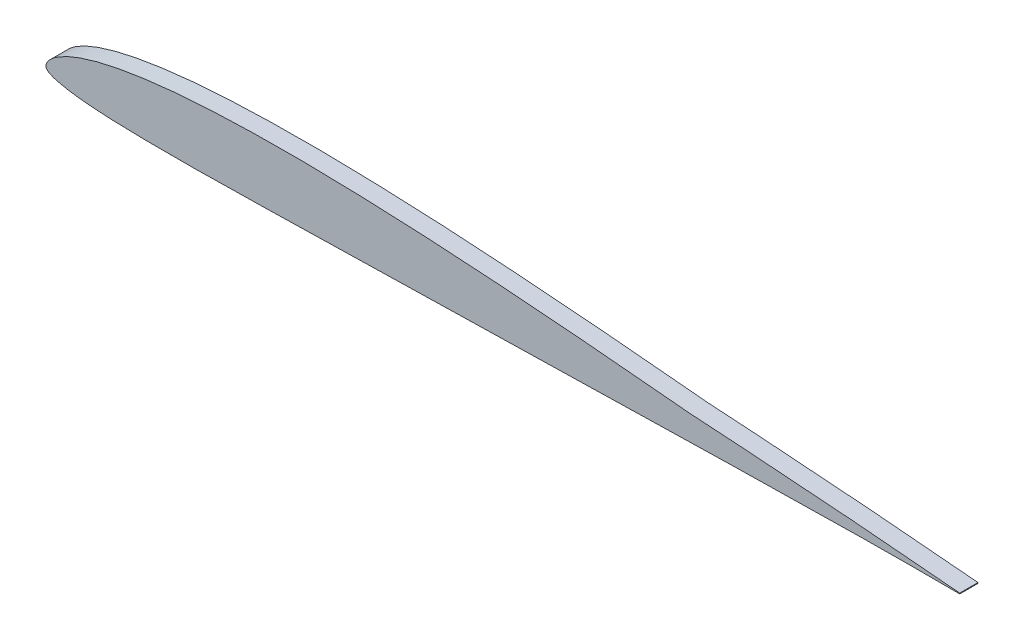
SolidWorks part; units mm, degrees
ref_plane "Front Plane" through (0, 0, 0) normal (0, 0, 1) x (1, 0, 0)
ref_plane "Top Plane" through (0, 0, 0) normal (0, 1, 0) x (1, 0, 0)
ref_plane "Right Plane" through (0, 0, 0) normal (1, 0, 0) x (0, 0, -1)
curve "Curve1"
  spline degree 3 poles (25.4, 0.0107, 0) (25.3506, 0.0152, 0) (25.2009, 0.0289, 0) (24.9376, 0.0531, 0) (24.6076, 0.082, 0) (24.2616, 0.1124, 0) (23.9125, 0.1431, 0) (23.5625, 0.1725, 0) (23.212, 0.2019, 0) (22.8613, 0.2307, 0) (22.5105, 0.2591, 0) (22.1596, 0.2869, 0) (21.8089, 0.314, 0) (21.4582, 0.3409, 0) (21.1077, 0.367, 0) (20.7573, 0.3928, 0) (20.407, 0.4182, 0) (20.0568, 0.4428, 0) (19.7068, 0.4673, 0) (19.3568, 0.4911, 0) (19.0069, 0.5145, 0) (18.6571, 0.5374, 0) (18.3335, 0.5583, 0) (18.0818, 0.5739, 0) (17.9246, 0.5843, 0) (17.8356, 0.5888, 0) (17.7472, 0.5983, 0) (17.5613, 0.6156, 0) (17.278, 0.6431, 0) (16.98, 0.6709, 0) (16.7137, 0.6956, 0) (16.4751, 0.7176, 0) (16.176, 0.7447, 0) (15.8267, 0.776, 0) (15.4701, 0.8073, 0) (15.1145, 0.838, 0) (14.7793, 0.8663, 0) (14.4495, 0.8936, 0) (14.1621, 0.9169, 0) (13.925, 0.9358, 0) (13.6642, 0.9563, 0) (13.3619, 0.9794, 0) (13.0103, 1.0056, 0) (12.659, 1.031, 0) (12.3077, 1.0554, 0) (11.9565, 1.0789, 0) (11.6054, 1.1014, 0) (11.2544, 1.1228, 0) (10.9034, 1.1432, 0) (10.5525, 1.1624, 0) (10.2016, 1.1803, 0) (9.8507, 1.197, 0) (9.5, 1.2123, 0) (9.1492, 1.2263, 0) (8.7986, 1.2386, 0) (8.448, 1.2494, 0) (8.0977, 1.2585, 0) (7.7474, 1.2658, 0) (7.3974, 1.2711, 0) (7.0475, 1.2745, 0) (6.6979, 1.2756, 0) (6.3485, 1.2744, 0) (5.9995, 1.2706, 0) (5.6509, 1.2642, 0) (5.3028, 1.2548, 0) (4.9554, 1.2422, 0) (4.6087, 1.2261, 0) (4.2629, 1.2062, 0) (3.9183, 1.1823, 0) (3.5751, 1.1536, 0) (3.2336, 1.12, 0) (2.8944, 1.0807, 0) (2.5581, 1.0351, 0) (2.2254, 0.9824, 0) (1.8975, 0.9214, 0) (1.5762, 0.8511, 0) (1.2643, 0.7698, 0) (0.9677, 0.6771, 0) (0.6972, 0.5737, 0) (0.4689, 0.4653, 0) (0.2948, 0.361, 0) (0.1747, 0.2696, 0) (0.0967, 0.1939, 0) (0.0471, 0.1311, 0) (0.0171, 0.0777, 0) (0.0019, 0.0319, 0) (-0.0016, -0.0085, 0) (0.0071, -0.0466, 0) (0.0322, -0.0832, 0) (0.0764, -0.1158, 0) (0.1405, -0.1489, 0) (0.2348, -0.1846, 0) (0.3747, -0.2244, 0) (0.5727, -0.265, 0) (0.8268, -0.3029, 0) (1.1218, -0.3343, 0) (1.4394, -0.3584, 0) (1.7684, -0.3763, 0) (2.1036, -0.389, 0) (2.4428, -0.3976, 0) (2.7846, -0.4031, 0) (3.1285, -0.4061, 0) (3.4739, -0.407, 0) (3.8205, -0.4061, 0) (4.168, -0.4035, 0) (4.5164, -0.3997, 0) (4.8654, -0.3948, 0) (5.2151, -0.389, 0) (5.5654, -0.3825, 0) (5.9165, -0.3755, 0) (6.2684, -0.368, 0) (6.621, -0.3604, 0) (6.9745, -0.3524, 0) (7.3287, -0.3442, 0) (7.6835, -0.336, 0) (8.039, -0.3276, 0) (8.3948, -0.3192, 0) (8.7511, -0.3108, 0) (9.1077, -0.3024, 0) (9.4646, -0.2939, 0) (9.8219, -0.2855, 0) (10.1795, -0.2771, 0) (10.5373, -0.2687, 0) (10.8952, -0.2603, 0) (11.2527, -0.252, 0) (11.6101, -0.2438, 0) (11.9672, -0.2355, 0) (12.3241, -0.2274, 0) (12.6807, -0.2193, 0) (13.0371, -0.2114, 0) (13.3934, -0.2033, 0) (13.6949, -0.1966, 0) (13.9592, -0.1908, 0) (14.1921, -0.1856, 0) (14.4749, -0.1792, 0) (14.7878, -0.1723, 0) (15.131, -0.1647, 0) (15.4754, -0.1569, 0) (15.8234, -0.1492, 0) (16.1349, -0.1423, 0) (16.4075, -0.1363, 0) (16.6379, -0.1313, 0) (16.9029, -0.1255, 0) (17.2072, -0.1189, 0) (17.4885, -0.1128, 0) (17.6791, -0.1088, 0) (17.7715, -0.1068, 0) (17.8501, -0.1053, 0) (18.0096, -0.1018, 0) (18.269, -0.0964, 0) (18.61, -0.0893, 0) (18.9621, -0.082, 0) (19.3141, -0.0749, 0) (19.666, -0.0678, 0) (20.0179, -0.0609, 0) (20.3698, -0.054, 0) (20.7219, -0.0473, 0) (21.074, -0.0408, 0) (21.4262, -0.0348, 0) (21.7784, -0.0292, 0) (22.1308, -0.0242, 0) (22.4832, -0.0197, 0) (22.8357, -0.0157, 0) (23.1883, -0.0125, 0) (23.5408, -0.0098, 0) (23.8935, -0.008, 0) (24.246, -0.0071, 0) (24.5963, -0.007, 0) (24.9308, -0.0084, 0) (25.198, -0.0096, 0) (25.3499, -0.0104, 0) (25.4, -0.0107, 0) knots 0 0 0 0 0.002901 0.008799 0.015478 0.022288 0.029131 0.035985 0.042847 0.049714 0.056581 0.063448 0.070313 0.077171 0.084031 0.090885 0.097737 0.104584 0.111432 0.118275 0.125116 0.131954 0.138793 0.144098 0.146709 0.148014 0.149313 0.151911 0.158945 0.165974 0.169425 0.174599 0.18 0.186998 0.195126 0.200949 0.20789 0.214818 0.220317 0.224762 0.228741 0.235631 0.242503 0.249376 0.256249 0.263115 0.269975 0.276837 0.283698 0.290553 0.297409 0.304262 0.311112 0.317958 0.324805 0.331647 0.338484 0.345319 0.352149 0.358974 0.365797 0.372613 0.37942 0.386225 0.393018 0.399801 0.406576 0.413331 0.420073 0.426793 0.433487 0.440154 0.446776 0.453353 0.459862 0.466294 0.472602 0.478718 0.484477 0.489534 0.493496 0.496331 0.498346 0.499841 0.500999 0.501915 0.502649 0.503345 0.504158 0.505185 0.506526 0.508376 0.511074 0.515031 0.520197 0.526109 0.532386 0.538838 0.545393 0.552019 0.558693 0.565404 0.572145 0.578909 0.585689 0.592488 0.599298 0.60612 0.612956 0.619809 0.626673 0.633554 0.640451 0.647364 0.654291 0.661227 0.668172 0.675126 0.682086 0.689049 0.69602 0.703 0.709987 0.71697 0.723948 0.73092 0.73789 0.744856 0.751814 0.758769 0.765721 0.77267 0.776424 0.78119 0.786305 0.792978 0.79951 0.806399 0.81314 0.819881 0.824633 0.829103 0.833367 0.840145 0.84692 0.849831 0.851305 0.852333 0.85443 0.860642 0.867519 0.87439 0.881257 0.888123 0.894989 0.901857 0.908727 0.915597 0.922469 0.929344 0.936217 0.943092 0.949972 0.956848 0.963729 0.970609 0.97749 0.984361 0.991109 0.997067 1 1 1 1
sketch "Sketch2" plane through (0, 0, 0) normal (0, 0, 1) x (1, 0, 0)
  line L0 (64.7182, -2.4991) -> (64.7182, -2.5635)
  line L1 (127, 0.0536) -> (127, -0.0536)
  spline S0 degree 3 poles (-80.1469, -1996.7005) (74.4105, -0.3887) (49.5476, -2.2151) (24.9376, 0.0531) (24.6076, 0.082) (24.2616, 0.1124) (23.9125, 0.1431) (23.5625, 0.1725) (23.212, 0.2019) (22.8613, 0.2307) (22.5105, 0.2591) (22.1596, 0.2869) (21.8089, 0.314) (21.4582, 0.3409) (21.1077, 0.367) (20.7573, 0.3928) (20.407, 0.4182) (20.0568, 0.4428) (19.7068, 0.4673) (19.3568, 0.4911) (19.0069, 0.5145) (18.6571, 0.5374) (18.3335, 0.5583) (18.0818, 0.5739) (17.9246, 0.5843) (17.8356, 0.5888) (17.7472, 0.5983) (17.5613, 0.6156) (17.278, 0.6431) (16.98, 0.6709) (16.7137, 0.6956) (16.4751, 0.7176) (16.176, 0.7447) (15.8267, 0.776) (15.4701, 0.8073) (15.1145, 0.838) (14.7793, 0.8663) (14.4495, 0.8936) (14.1621, 0.9169) (13.925, 0.9358) (13.6642, 0.9563) (13.3619, 0.9794) (13.0103, 1.0056) (12.659, 1.031) (12.1907, 1.0635) (11.7225, 1.0942) (11.2544, 1.1228) (10.9034, 1.1432) (10.4356, 1.1688) (9.9677, 1.1919) (9.5, 1.2123) (9.1492, 1.2263) (8.7986, 1.2386) (8.448, 1.2494) (8.0977, 1.2585) (7.7474, 1.2658) (7.3974, 1.2711) (7.0475, 1.2745) (6.6979, 1.2756) (6.3485, 1.2744) (5.9995, 1.2706) (5.6509, 1.2642) (5.3028, 1.2548) (4.9554, 1.2422) (4.6087, 1.2261) (4.2629, 1.2062) (3.9183, 1.1823) (3.5751, 1.1536) (3.2336, 1.12) (2.8944, 1.0807) (2.5581, 1.0351) (2.2254, 0.9824) (1.8975, 0.9214) (1.5762, 0.8511) (1.2643, 0.7698) (0.9677, 0.6771) (0.6972, 0.5737) (0.4689, 0.4653) (0.2948, 0.361) (0.1747, 0.2696) (0.0967, 0.1939) (0.0471, 0.1311) (0.0171, 0.0777) (0.0019, 0.0319) (-0.0016, -0.0085) (0.0071, -0.0466) (0.0322, -0.0832) (0.0764, -0.1158) (0.1405, -0.1489) (0.2348, -0.1846) (0.3747, -0.2244) (0.5727, -0.265) (0.8268, -0.3029) (1.1218, -0.3343) (1.4394, -0.3584) (1.7684, -0.3763) (2.1036, -0.389) (2.4428, -0.3976) (2.7846, -0.4031) (3.1285, -0.4061) (3.4739, -0.407) (3.8205, -0.4061) (4.168, -0.4035) (4.5164, -0.3997) (4.8654, -0.3948) (5.2151, -0.389) (5.5654, -0.3825) (5.9165, -0.3755) (6.2684, -0.368) (6.621, -0.3604) (6.9745, -0.3524) (7.3287, -0.3442) (7.8022, -0.3332) (8.2764, -0.322) (8.7511, -0.3108) (9.1077, -0.3024) (9.4646, -0.2939) (9.8219, -0.2855) (10.1795, -0.2771) (10.5373, -0.2687) (10.8952, -0.2603) (11.2527, -0.252) (11.6101, -0.2438) (11.9672, -0.2355) (12.3241, -0.2274) (12.6807, -0.2193) (13.0371, -0.2114) (13.3934, -0.2033) (13.6949, -0.1966) (14.0466, -0.1889) (14.3934, -0.181) (14.7878, -0.1723) (15.131, -0.1647) (15.4754, -0.1569) (15.8234, -0.1492) (16.1349, -0.1423) (16.4075, -0.1363) (16.6379, -0.1313) (16.9029, -0.1255) (17.2072, -0.1189) (17.4885, -0.1128) (17.6791, -0.1088) (17.7715, -0.1068) (17.8501, -0.1053) (18.0096, -0.1018) (18.269, -0.0964) (18.61, -0.0893) (18.9621, -0.082) (19.3141, -0.0749) (19.666, -0.0678) (20.0179, -0.0609) (20.3698, -0.054) (20.7219, -0.0473) (21.074, -0.0408) (21.4262, -0.0348) (21.8959, -0.0274) (22.3658, -0.021) (22.8357, -0.0157) (23.1883, -0.0125) (23.5408, -0.0098) (23.8935, -0.008) (24.246, -0.0071) (24.5963, -0.007) (24.9308, -0.0084) (48.8353, -0.1171) (72.6037, -4.5166) (105.9787, 1997.8631) knots -1.431006 -1.431006 -1.431006 -1.431006 0.002901 0.008799 0.015478 0.022288 0.029131 0.035985 0.042847 0.049714 0.056581 0.063448 0.070313 0.077171 0.084031 0.090885 0.097737 0.104584 0.111432 0.118275 0.125116 0.131954 0.138793 0.144098 0.146709 0.148014 0.149313 0.151911 0.158945 0.165974 0.169425 0.174599 0.18 0.186998 0.195126 0.200949 0.20789 0.214818 0.220317 0.224762 0.228741 0.235631 0.242503 0.249376 0.256249 0.269975 0.276837 0.283698 0.290553 0.304262 0.311112 0.317958 0.324805 0.331647 0.338484 0.345319 0.352149 0.358974 0.365797 0.372613 0.37942 0.386225 0.393018 0.399801 0.406576 0.413331 0.420073 0.426793 0.433487 0.440154 0.446776 0.453353 0.459862 0.466294 0.472602 0.478718 0.484477 0.489534 0.493496 0.496331 0.498346 0.499841 0.500999 0.501915 0.502649 0.503345 0.504158 0.505185 0.506526 0.508376 0.511074 0.515031 0.520197 0.526109 0.532386 0.538838 0.545393 0.552019 0.558693 0.565404 0.572145 0.578909 0.585689 0.592488 0.599298 0.60612 0.612956 0.619809 0.626673 0.633554 0.640451 0.647364 0.654291 0.668172 0.675126 0.682086 0.689049 0.69602 0.703 0.709987 0.71697 0.723948 0.73092 0.73789 0.744856 0.751814 0.758769 0.765721 0.77267 0.776424 0.786305 0.792978 0.79951 0.806399 0.81314 0.819881 0.824633 0.829103 0.833367 0.840145 0.84692 0.849831 0.851305 0.852333 0.85443 0.860642 0.867519 0.87439 0.881257 0.888123 0.894989 0.901857 0.908727 0.915597 0.922469 0.929344 0.943092 0.949972 0.956848 0.963729 0.970609 0.97749 0.984361 0.991109 0.997067 2.383465 2.383465 2.383465 2.383465 only from (25.4, 0.0107) to (25.4, -0.0107) construction
  spline S1 degree 3 poles (25.4, 0.0107) (25.3506, 0.0152) (25.2009, 0.0289) (24.9376, 0.0531) (24.6076, 0.082) (24.2616, 0.1124) (23.9125, 0.1431) (23.5625, 0.1725) (23.212, 0.2019) (22.8613, 0.2307) (22.5105, 0.2591) (22.1596, 0.2869) (21.8089, 0.314) (21.4582, 0.3409) (21.1077, 0.367) (20.7573, 0.3928) (20.407, 0.4182) (20.0568, 0.4428) (19.7068, 0.4673) (19.3568, 0.4911) (19.0069, 0.5145) (18.6571, 0.5374) (18.3335, 0.5583) (18.0818, 0.5739) (17.9246, 0.5843) (17.8356, 0.5888) (17.7472, 0.5983) (17.5613, 0.6156) (17.278, 0.6431) (16.98, 0.6709) (16.7137, 0.6956) (16.4751, 0.7176) (16.176, 0.7447) (15.8267, 0.776) (15.4701, 0.8073) (15.1145, 0.838) (14.7793, 0.8663) (14.4495, 0.8936) (14.1621, 0.9169) (13.925, 0.9358) (13.6642, 0.9563) (13.3619, 0.9794) (13.0103, 1.0056) (12.659, 1.031) (12.1907, 1.0635) (11.7225, 1.0942) (11.2544, 1.1228) (10.9034, 1.1432) (10.4356, 1.1688) (9.9677, 1.1919) (9.5, 1.2123) (9.1492, 1.2263) (8.7986, 1.2386) (8.448, 1.2494) (8.0977, 1.2585) (7.7474, 1.2658) (7.3974, 1.2711) (7.0475, 1.2745) (6.6979, 1.2756) (6.3485, 1.2744) (5.9995, 1.2706) (5.6509, 1.2642) (5.3028, 1.2548) (4.9554, 1.2422) (4.6087, 1.2261) (4.2629, 1.2062) (3.9183, 1.1823) (3.5751, 1.1536) (3.2336, 1.12) (2.8944, 1.0807) (2.5581, 1.0351) (2.2254, 0.9824) (1.8975, 0.9214) (1.5762, 0.8511) (1.2643, 0.7698) (0.9677, 0.6771) (0.6972, 0.5737) (0.4689, 0.4653) (0.2948, 0.361) (0.1747, 0.2696) (0.0967, 0.1939) (0.0471, 0.1311) (0.0171, 0.0777) (0.0019, 0.0319) (-0.0016, -0.0085) (0.0071, -0.0466) (0.0322, -0.0832) (0.0764, -0.1158) (0.1405, -0.1489) (0.2348, -0.1846) (0.3747, -0.2244) (0.5727, -0.265) (0.8268, -0.3029) (1.1218, -0.3343) (1.4394, -0.3584) (1.7684, -0.3763) (2.1036, -0.389) (2.4428, -0.3976) (2.7846, -0.4031) (3.1285, -0.4061) (3.4739, -0.407) (3.8205, -0.4061) (4.168, -0.4035) (4.5164, -0.3997) (4.8654, -0.3948) (5.2151, -0.389) (5.5654, -0.3825) (5.9165, -0.3755) (6.2684, -0.368) (6.621, -0.3604) (6.9745, -0.3524) (7.3287, -0.3442) (7.8022, -0.3332) (8.2764, -0.322) (8.7511, -0.3108) (9.1077, -0.3024) (9.4646, -0.2939) (9.8219, -0.2855) (10.1795, -0.2771) (10.5373, -0.2687) (10.8952, -0.2603) (11.2527, -0.252) (11.6101, -0.2438) (11.9672, -0.2355) (12.3241, -0.2274) (12.6807, -0.2193) (13.0371, -0.2114) (13.3934, -0.2033) (13.6949, -0.1966) (14.0466, -0.1889) (14.3934, -0.181) (14.7878, -0.1723) (15.131, -0.1647) (15.4754, -0.1569) (15.8234, -0.1492) (16.1349, -0.1423) (16.4075, -0.1363) (16.6379, -0.1313) (16.9029, -0.1255) (17.2072, -0.1189) (17.4885, -0.1128) (17.6791, -0.1088) (17.7715, -0.1068) (17.8501, -0.1053) (18.0096, -0.1018) (18.269, -0.0964) (18.61, -0.0893) (18.9621, -0.082) (19.3141, -0.0749) (19.666, -0.0678) (20.0179, -0.0609) (20.3698, -0.054) (20.7219, -0.0473) (21.074, -0.0408) (21.4262, -0.0348) (21.8959, -0.0274) (22.3658, -0.021) (22.8357, -0.0157) (23.1883, -0.0125) (23.5408, -0.0098) (23.8935, -0.008) (24.246, -0.0071) (24.5963, -0.007) (24.9308, -0.0084) (25.198, -0.0096) (25.3499, -0.0104) (25.4, -0.0107) knots 0 0 0 0 0.002901 0.008799 0.015478 0.022288 0.029131 0.035985 0.042847 0.049714 0.056581 0.063448 0.070313 0.077171 0.084031 0.090885 0.097737 0.104584 0.111432 0.118275 0.125116 0.131954 0.138793 0.144098 0.146709 0.148014 0.149313 0.151911 0.158945 0.165974 0.169425 0.174599 0.18 0.186998 0.195126 0.200949 0.20789 0.214818 0.220317 0.224762 0.228741 0.235631 0.242503 0.249376 0.256249 0.269975 0.276837 0.283698 0.290553 0.304262 0.311112 0.317958 0.324805 0.331647 0.338484 0.345319 0.352149 0.358974 0.365797 0.372613 0.37942 0.386225 0.393018 0.399801 0.406576 0.413331 0.420073 0.426793 0.433487 0.440154 0.446776 0.453353 0.459862 0.466294 0.472602 0.478718 0.484477 0.489534 0.493496 0.496331 0.498346 0.499841 0.500999 0.501915 0.502649 0.503345 0.504158 0.505185 0.506526 0.508376 0.511074 0.515031 0.520197 0.526109 0.532386 0.538838 0.545393 0.552019 0.558693 0.565404 0.572145 0.578909 0.585689 0.592488 0.599298 0.60612 0.612956 0.619809 0.626673 0.633554 0.640451 0.647364 0.654291 0.668172 0.675126 0.682086 0.689049 0.69602 0.703 0.709987 0.71697 0.723948 0.73092 0.73789 0.744856 0.751814 0.758769 0.765721 0.77267 0.776424 0.786305 0.792978 0.79951 0.806399 0.81314 0.819881 0.824633 0.829103 0.833367 0.840145 0.84692 0.849831 0.851305 0.852333 0.85443 0.860642 0.867519 0.87439 0.881257 0.888123 0.894989 0.901857 0.908727 0.915597 0.922469 0.929344 0.943092 0.949972 0.956848 0.963729 0.970609 0.97749 0.984361 0.991109 0.997067 1 1 1 1
  spline S2 degree 3 poles (127, 0.0536) (126.7532, 0.0761) (126.0046, 0.1443) (124.6879, 0.2657) (123.038, 0.4099) (121.3078, 0.5622) (119.5626, 0.7154) (117.8125, 0.8626) (116.0602, 1.0096) (114.3066, 1.1533) (112.5524, 1.2954) (110.7981, 1.4344) (109.0444, 1.5698) (107.2911, 1.7045) (105.5386, 1.8351) (103.7864, 1.9642) (102.0351, 2.0908) (100.2841, 2.214) (98.5339, 2.3364) (96.7839, 2.4555) (95.0347, 2.5723) (93.2856, 2.6871) (91.6673, 2.7916) (90.4092, 2.8696) (89.6232, 2.9215) (89.1782, 2.9441) (88.7362, 2.9915) (87.8065, 3.0778) (86.3898, 3.2155) (84.9001, 3.3545) (83.5684, 3.478) (82.3753, 3.5879) (80.8802, 3.7236) (79.1336, 3.8802) (77.3507, 4.0366) (75.5725, 4.1898) (73.8963, 4.3315) (72.2474, 4.4682) (70.8107, 4.5845) (69.625, 4.6789) (68.3208, 4.7815) (66.8096, 4.8971) (65.0517, 5.0279) (63.2949, 5.1548) (60.9536, 5.3176) (58.6126, 5.471) (56.2721, 5.6142) (54.5172, 5.7159) (52.1778, 5.8439) (49.8387, 5.9596) (47.4998, 6.0617) (45.7461, 6.1315) (43.9929, 6.1932) (42.2402, 6.247) (40.4883, 6.2924) (38.7372, 6.3291) (36.987, 6.3557) (35.2377, 6.3726) (33.4894, 6.3781) (31.7426, 6.3719) (29.9976, 6.3531) (28.2547, 6.321) (26.5142, 6.274) (24.7768, 6.2109) (23.0433, 6.1307) (21.3143, 6.0312) (19.5913, 5.9114) (17.8753, 5.7682) (16.1681, 5.6002) (14.4722, 5.4034) (12.7903, 5.1755) (11.1272, 4.9119) (9.4877, 4.6072) (7.881, 4.2554) (6.3217, 3.8492) (4.8384, 3.3854) (3.4862, 2.8684) (2.3443, 2.3263) (1.4738, 1.805) (0.8733, 1.3482) (0.4835, 0.9696) (0.2355, 0.6556) (0.0854, 0.3886) (0.0093, 0.1593) (-0.0082, -0.0427) (0.0354, -0.2332) (0.1608, -0.4161) (0.3818, -0.5789) (0.7024, -0.7445) (1.1738, -0.9231) (1.8733, -1.1219) (2.8634, -1.3251) (4.1342, -1.5144) (5.6088, -1.6713) (7.1969, -1.7921) (8.842, -1.8815) (10.5181, -1.945) (12.2138, -1.9881) (13.9231, -2.0156) (15.6423, -2.0306) (17.3693, -2.0352) (19.1023, -2.0304) (20.8402, -2.0177) (22.5819, -1.9987) (24.3271, -1.9739) (26.0754, -1.9449) (27.8272, -1.9125) (29.5827, -1.8776) (31.342, -1.84) (33.1051, -1.8019) (34.8723, -1.7618) (36.6433, -1.721) (39.0109, -1.666) (41.3818, -1.6098) (43.7556, -1.5538) (45.5386, -1.5118) (47.323, -1.4696) (49.1093, -1.4276) (50.8974, -1.3853) (52.6867, -1.3435) (54.4758, -1.3017) (56.2636, -1.2601) (58.0503, -1.2192) (59.836, -1.1776) (61.6205, -1.1372) (63.4036, -1.0967) (65.1856, -1.0568) (66.9668, -1.0167) (68.4747, -0.9832) (70.2328, -0.9443) (71.9672, -0.9051) (73.939, -0.8615) (75.6551, -0.8234) (77.3771, -0.7847) (79.117, -0.7461) (80.6743, -0.7116) (82.0377, -0.6816) (83.1895, -0.6565) (84.5144, -0.6274) (86.0361, -0.5947) (87.4423, -0.5642) (88.3955, -0.5441) (88.8577, -0.534) (89.2506, -0.5265) (90.048, -0.509) (91.3451, -0.4819) (93.0499, -0.4463) (94.8107, -0.4101) (96.5705, -0.3747) (98.3298, -0.3392) (100.0893, -0.3047) (101.8492, -0.27) (103.6094, -0.2366) (105.3699, -0.2038) (107.1309, -0.1742) (109.4795, -0.1369) (111.8288, -0.1051) (114.1784, -0.0783) (115.9413, -0.0623) (117.7042, -0.0489) (119.4676, -0.04) (121.2302, -0.0356) (122.9815, -0.0349) (124.6538, -0.0418) (125.9899, -0.0478) (126.7494, -0.0522) (127, -0.0536) knots 0 0 0 0 0.002901 0.008799 0.015478 0.022288 0.029131 0.035985 0.042847 0.049714 0.056581 0.063448 0.070313 0.077171 0.084031 0.090885 0.097737 0.104584 0.111432 0.118275 0.125116 0.131954 0.138793 0.144098 0.146709 0.148014 0.149313 0.151911 0.158945 0.165974 0.169425 0.174599 0.18 0.186998 0.195126 0.200949 0.20789 0.214818 0.220317 0.224762 0.228741 0.235631 0.242503 0.249376 0.256249 0.269975 0.276837 0.283698 0.290553 0.304262 0.311112 0.317958 0.324805 0.331647 0.338484 0.345319 0.352149 0.358974 0.365797 0.372613 0.37942 0.386225 0.393018 0.399801 0.406576 0.413331 0.420073 0.426793 0.433487 0.440154 0.446776 0.453353 0.459862 0.466294 0.472602 0.478718 0.484477 0.489534 0.493496 0.496331 0.498346 0.499841 0.500999 0.501915 0.502649 0.503345 0.504158 0.505185 0.506526 0.508376 0.511074 0.515031 0.520197 0.526109 0.532386 0.538838 0.545393 0.552019 0.558693 0.565404 0.572145 0.578909 0.585689 0.592488 0.599298 0.60612 0.612956 0.619809 0.626673 0.633554 0.640451 0.647364 0.654291 0.668172 0.675126 0.682086 0.689049 0.69602 0.703 0.709987 0.71697 0.723948 0.73092 0.73789 0.744856 0.751814 0.758769 0.765721 0.77267 0.776424 0.786305 0.792978 0.79951 0.806399 0.81314 0.819881 0.824633 0.829103 0.833367 0.840145 0.84692 0.849831 0.851305 0.852333 0.85443 0.860642 0.867519 0.87439 0.881257 0.888123 0.894989 0.901857 0.908727 0.915597 0.922469 0.929344 0.943092 0.949972 0.956848 0.963729 0.970609 0.97749 0.984361 0.991109 0.997067 1 1 1 1
extrude "Boss-Extrude1" add sketch "Sketch2" along normal mid plane 2.54
